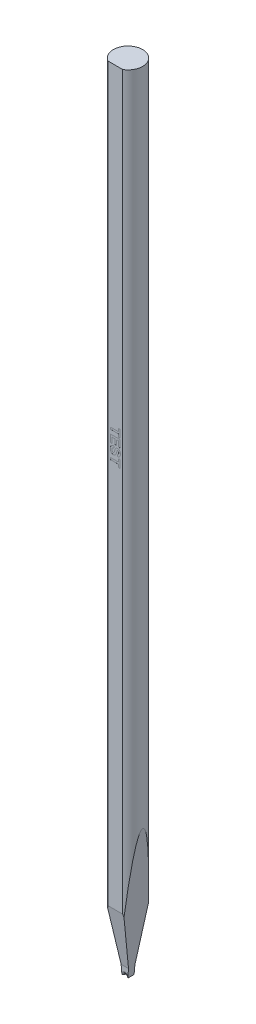
SolidWorks part; units mm, degrees
ref_plane "Ebene vorne" through (0, 0, 0) normal (0, 0, 1) x (1, 0, 0)
ref_plane "Ebene oben" through (0, 0, 0) normal (0, 1, 0) x (1, 0, 0)
ref_plane "Ebene rechts" through (0, 0, 0) normal (1, 0, 0) x (0, 0, -1)
sketch "sketch_TL_cutting" plane through (0, 0, 0) normal (0, 1, 0) x (1, 0, 0)
  circle A0 centre (0, 0) radius 1.4986
extrude "TL_cutting" add sketch "sketch_TL_cutting" along normal blind 81.28
sketch "sketch_TDF_grinding" plane through (0, 0, 0) normal (0, 1, 0) x (1, 0, 0)
  line L0 (0, 0) -> (0, -1.2954) construction
  line L1 (-1.5086, -4.3126) -> (1.5086, -4.3126)
  line L2 (-1.5086, -4.3126) -> (-1.5086, -1.2954)
  line L3 (-1.5086, -1.2954) -> (1.5086, -1.2954)
  line L4 (1.5086, -4.3126) -> (1.5086, -1.2954)
  circle A1 centre (0, 0) radius 1.4986 construction
  point P9 (0, -4.3126)
  dimension "TD_2Offset_X" = 3.0172
  dimension "TD_2Offset_Z" = 3.0172
extrude "TDF_grinding" cut sketch "sketch_TDF_grinding" along normal through all
sketch "sketch_engraving" plane through (0, 0, 1.2954) normal (0, 0, 1) x (1, 0, 0)
  line L0 (0.7535, 81.28) -> (-0.7535, 81.28) construction
  line L6 (-0.7535, 0) -> (0.7535, 0) construction
  line L7 (0, 0) -> (0, 49.28) construction
  line L8 (-0.5, 49.28) -> (-0.5, 0) construction
  text T0 "TEST" font "Arial" height 1
  dimension "D2" = 0.5
  dimension "EngravingStart" = 32
extrude "engraving" cut sketch "sketch_engraving" against normal blind 0.005
sketch "sketch_VW_VR_grinding" plane through (0, 0, 0) normal (0, 0, 1) x (1, 0, 0)
  line L0 (-1.4936, -0.01) -> (-1.4936, 0.874)
  line L1 (1.4936, -0.01) -> (1.4936, 0.874)
  line L2 (-1.4936, 0) -> (1.4936, 0) construction
  line L3 (-1.5086, 0.879) -> (-1.4986, 0.879)
  line L4 (1.4986, 0.879) -> (1.5086, 0.879)
  line L5 (-1.5086, 0.879) -> (-1.5086, -0.01)
  line L6 (-1.5086, -0.01) -> (-1.4936, -0.01)
  line L7 (1.4936, -0.01) -> (1.5086, -0.01)
  line L8 (1.5086, -0.01) -> (1.5086, 0.879)
  line L9 (-1.4986, 0.879) -> (-1.4986, 0.874) construction
  line L10 (-1.4936, 0.874) -> (-1.4986, 0.874) construction
  line L11 (1.4936, 0.874) -> (1.4986, 0.874) construction
  line L12 (1.4986, 0.879) -> (1.4986, 0.874) construction
  arc A0 (-1.4986, 0.879) -> (-1.4936, 0.874) centre (-1.4986, 0.874) cw
  arc A2 (1.4936, 0.874) -> (1.4986, 0.879) centre (1.4986, 0.874) cw
  dimension "D1" = 0.01
  dimension "D4" = 3.0172
extrude "VW_VR_grinding" cut sketch "sketch_VW_VR_grinding" against normal blind 1.5086 and the other way blind 1.5086
sketch "sketch_ISA_grinding" plane through (0, 0, 0) normal (0, 0, 1) x (1, 0, 0)
  line L0 (-0.2997, 0) -> (-1.5086, 13.8176)
  line L4 (1.5086, 13.8176) -> (0.2997, 0)
  line L5 (0.2997, 0) -> (-0.2997, 0)
  line L6 (0, 0) -> (0, 30.49) construction
  line L7 (-1.5086, 13.8176) -> (-1.5086, -0.01)
  line L12 (-1.5086, -0.01) -> (1.5086, -0.01)
  line L13 (1.5086, -0.01) -> (1.5086, 13.8176)
  dimension "ISA" = 10
  dimension "TD_2Offset" = 3.0172
  dimension "Offset" = 0.01
extrude "ISA_grinding" cut sketch "sketch_ISA_grinding" against normal blind 1.5086 and the other way blind 1.5086
sketch "sketch_pre_FRX_BRX" plane through (0, 0, 0) normal (1, 0, 0) x (0, 0, -1)
  line L0 (1.4986, -0.01) -> (1.4986, 3.9152) construction
  line L1 (-1.2954, -0.01) -> (-1.2954, 0.879) construction
  line L2 (-0.3251, -0.01) -> (-0.3251, 0.879)
  line L3 (-0.3251, 0.879) -> (-1.5086, 0.879)
  line L4 (-1.5086, 0.879) -> (-1.5086, -0.01)
  line L5 (-1.5086, -0.01) -> (-0.3251, -0.01)
  line L6 (0.3251, -0.01) -> (0.3251, 0.879)
  line L7 (0.3251, 0.879) -> (1.5086, 0.879)
  line L8 (1.5086, 0.879) -> (1.5086, -0.01)
  line L9 (1.5086, -0.01) -> (0.3251, -0.01)
  dimension "D3" = 0.01
  dimension "D4" = 0.889
  dimension "D5" = 3.0172
  dimension "D6" = 0.6502
  dimension "D2" = 0.01
  dimension "D7" = 1.8237
extrude "pre_FRX_BRX" cut sketch "sketch_pre_FRX_BRX" against normal blind 1.5086 and the other way blind 1.5086
sketch "sketch_contour_V-Groove" plane through (0, 0, 0) normal (1, 0, 0) x (0, 0, -1)
  line L0 (-1.2954, 0.1905) -> (0, 0.1905)
  line L1 (0, 0.1905) -> (1.4986, 0.1905)
  line L2 (1.4986, -0.8411) -> (1.4986, 1.3178) construction
  line L3 (-1.2954, -0.9209) -> (-1.2954, 1.9363) construction
  line L4 (-1.2954, 0) -> (1.4986, 0) construction
  line L5 (0.3251, 0) -> (0.3251, 0.1905) construction
  line L6 (-0.3251, 0) -> (-0.3251, 0.1905) construction
  dimension "D1" = 0
ref_plane "front" through (0, 0, 1.2954) normal (0, 0, 1) x (1, 0, 0)
ref_plane "back" through (0, 0, -1.4986) normal (0, 0, 1) x (1, 0, 0)
sketch "sketch_section_V-Groove" plane through (0, 0, 1.2954) normal (0, 0, 1) x (1, 0, 0)
  line L0 (-1.499, -1.905) -> (-0.0499, 0.1645)
  line L2 (0.0499, 0.1645) -> (1.499, -1.905)
  line L3 (-1.499, -1.905) -> (1.499, -1.905)
  line L4 (0, -1.905) -> (0, 0.1905) construction
  line L5 (-0.1651, 0) -> (0.1651, 0) construction
  arc A0 (0.0499, 0.1645) -> (-0.0499, 0.1645) centre (0, 0.1296) ccw
  dimension "GA" = 70
sweep "V-Groove_EDM" cut profiles "sketch_section_V-Groove" path "sketch_contour_V-Groove"
fillet "FR_EDM" radius 0.2261 3 edges at (0.1075, 0.0823, 0.3251) (0, 0.1905, 0.3251) (-0.1075, 0.0823, 0.3251)
fillet "BR_EDM" radius 0.2261 3 edges at (0.1075, 0.0823, -0.3251) (0, 0.1905, -0.3251) (-0.1075, 0.0823, -0.3251)
sketch "sketch_FA_BA_grinding" plane through (0, 0, 0) normal (1, 0, 0) x (0, 0, -1)
  line L2 (2.4986, 13.2154) -> (2.4986, -0.1)
  line L3 (2.4986, -0.1) -> (0.3251, -0.1)
  line L5 (0.3251, -0.1) -> (0.3251, 0.889)
  line L6 (0.3251, 0.889) -> (2.4986, 13.2154)
  line L7 (1.4986, -0.1) -> (1.4986, 7.5441) construction
  line L8 (-1.2954, 6.3917) -> (-1.2954, -0.1) construction
  line L9 (-4.003, 21.7474) -> (-0.3251, 0.889)
  line L10 (-0.3251, 0.889) -> (-0.3251, -0.1)
  line L11 (-0.3251, -0.1) -> (-4.003, -0.1)
  line L12 (-4.003, -0.1) -> (-4.003, 21.7474)
  line L13 (-0.3251, 0.889) -> (0.3251, 0.889) construction
  dimension "D4" = 1
  dimension "D1" = 0.1
  dimension "FA" = 10
  dimension "BA" = 10
extrude "FA_BA_grinding" cut sketch "sketch_FA_BA_grinding" against normal blind 1.5086 and the other way blind 1.5086
sketch "sketch_groove_dimensions" plane through (0, 0, 0) normal (1, 0, 0) x (0, 0, -1)
  line L0 (-0.0991, 0.1905) -> (0.0991, 0.1905)
  line L1 (-0.3251, 0) -> (-0.3251, 0.4166) construction
  line L2 (1.4986, 0) -> (1.4986, 0.4166) construction
  line L3 (0.3251, 0) -> (0.3251, 0.4166) construction
  line L4 (-1.2954, 0) -> (-1.2954, 0.3999) construction
  arc A0 (0.0991, 0.1905) -> (0.3251, 0.4166) centre (0.0991, 0.4166) ccw
  arc A1 (-0.0991, 0.1905) -> (-0.3251, 0.4166) centre (-0.0991, 0.4166) cw
equation "\"_Offset\"=0.01mm"
equation "\"TL\"=81.28mm"
equation "\"TD\"=2.9972mm"
equation "\"TDF\"=2.794mm"
equation "\"BA\"=10deg"
equation "\"ISA\"=10deg"
equation "\"FA\"=10deg"
equation "\"GR\"=0.06096mm"
equation "\"GA\"=70deg"
equation "\"GD\"=0.1905mm"
equation "\"FL\"=0.65024mm"
equation "\"F\"=0.35052mm"
equation "\"FX\"=0mm"
equation "\"B\"=0.3302mm"
equation "\"VW\"=0mm"
equation "\"cleaned_VR\"= IIF ( \"VR\" > 0 , \"VR\" , \"E\" - \"_Offset\" )"
equation "\"cleaned_VW\"= IIF ( \"VW\" > 0 , \"VW\" , \"TD\" - \"_Offset\" )"
equation "\"back_edge\"= \"TD\" / 2 - \"X\""
equation "\"side_edge_Offset\"= \"TD\" / 2 + \"_Offset\""
equation "\"TD@sketch_TL_cutting\"=\"TD\""
equation "\"TL@TL_cutting\"=\"TL\""
equation "\"TDF@sketch_TDF_grinding\"=\"TDF\""
equation "\"TD_2Offset_X@sketch_TDF_grinding\"=\"TD\"+2*\"_Offset\""
equation "\"TD_2Offset_Z@sketch_TDF_grinding\"=\"TD\"+2*\"_Offset\""
equation "\"TL_Offset\"= \"TL\" + \"_Offset\""
equation "\"ISA@sketch_ISA_grinding\"=\"ISA\""
equation "\"W@sketch_ISA_grinding\"=\"W\""
equation "\"TD_2Offset@sketch_ISA_grinding\"=\"TD\"+2*\"_Offset\""
equation "\"Offset@sketch_ISA_grinding\"=\"_Offset\""
equation "\"05TD_Offset_posZ@ISA_grinding\"=\"side_edge_Offset\""
equation "\"05TD_Offset_negZ@ISA_grinding\"=\"side_edge_Offset\""
equation "\"E\"=0.889mm"
equation "\"cleaned_X\"= IIF ( \"X\" > 0 , \"X\" , \"TD\" / 2 - \"FL\" / 2 )"
equation "\"FR\"=0.22606mm"
equation "\"BR\"=0.22606mm"
equation "\"D1\"= \"side_edge_Offset\""
equation "\"D2\"= \"side_edge_Offset\""
equation "\"TDF@sketch_FA_BA_grinding\" = \"TDF\""
equation "\"FL@sketch_FA_BA_grinding\"=\"FL\""
equation "\"E@sketch_FA_BA_grinding\" = \"E\""
equation "\"D1@FA_BA_grinding\"=\"side_edge_Offset\""
equation "\"D2@FA_BA_grinding\"=\"side_angle_Offset\""
equation "\"10GD@sketch_section_V-Groove\" = 10 * \"GD\""
equation "\"GA@sketch_section_V-Groove\" = \"GA\""
equation "\"GD@sketch_section_V-Groove\" = \"GD\""
equation "\"B@sketch_section_V-Groove\" = \"B\""
equation "\"GD@sketch_contour_V-Groove\" = \"GD\""
equation "\"cleaned_FRX\"= IIF ( \"FRX\" > 0 , \"FRX\" , \"FR\" )"
equation "\"cleaned_BRX\"= IIF ( \"BRX\" > 0 , \"BRX\" , \"BR\" )"
equation "\"FL_groove_angle\"=0deg"
equation "\"D3@sketch_pre_FRX_BRX\" = \"_Offset\""
equation "\"D4@sketch_pre_FRX_BRX\" = \"E\""
equation "\"D5@sketch_pre_FRX_BRX\" = 2 * \"side_edge_Offset\""
equation "\"D6@sketch_pre_FRX_BRX\" = \"FL\" + ( \"FR\" - \"cleaned_FRX\" ) + ( \"BR\" - \"cleaned_BRX\" )"
equation "\"TD/2@sketch_pre_FRX_BRX\" = \"TD\" / 2"
equation "\"TDF@sketch_pre_FRX_BRX\" = \"TDF\""
equation "\"D2@sketch_pre_FRX_BRX\" = \"_Offset\""
equation "\"D1@pre_FRX_BRX\" = \"side_edge_Offset\""
equation "\"D2@pre_FRX_BRX\" = \"side_edge_Offset\""
equation "\"D1@BR_EDM\"=\"BR\""
equation "\"TD/2@sketch_FA_BA_grinding\" = \"TD\" / 2"
equation "\"TD/2@sketch_contour_V-Groove\" = \"TD\" / 2"
equation "\"TDF@sketch_contour_V-Groove\" = \"TDF\""
equation "\"D1@sketch_contour_V-Groove\"=\"FL_groove_angle\""
equation "\"FL@sketch_contour_V-Groove\"=\"FL\""
equation "\"FL/2@sketch_contour_V-Groove\" = \"FL\" / 2"
equation "\"D1@FR_EDM\"=\"FR\""
equation "\"D1@sketch_VW_VR_grinding\" = \"_Offset\""
equation "\"D4@sketch_VW_VR_grinding\" = 2 * \"side_edge_Offset\""
equation "\"VR@sketch_VW_VR_grinding\" = \"cleaned_VR\""
equation "\"VW@sketch_VW_VR_grinding\"=\"cleaned_VW\""
equation "\"D1@VW_VR_grinding\" = \"side_edge_Offset\""
equation "\"D2@VW_VR_grinding\" = \"side_edge_Offset\""
equation "\"X\"=0mm"
equation "\"VR\"=0mm"
equation "\"W\"=0.59944mm"
equation "\"VW_radius\"= \"cleaned_VW\" / 10"
equation "\"VW_radius_cleaned\"= IIF ( \"VW\" > 0 , \"VW_radius\" , \"_Offset\" / 2 )"
equation "\"D2@sketch_VW_VR_grinding\"=\"VW_radius_cleaned\""
equation "\"FRX\"=0mm"
equation "\"BRX\"=0mm"
equation "\"FA@sketch_FA_BA_grinding\" = \"FA\""
equation "\"D4@sketch_FA_BA_grinding\"=\"_Offset\"*100"
equation "\"BA@sketch_FA_BA_grinding\" = \"BA\""
equation "\"D1@sketch_groove_dimensions\" = \"TD\" / 2"
equation "\"FL@sketch_groove_dimensions\" = \"FL\""
equation "\"FR@sketch_groove_dimensions\" = \"FR\""
equation "\"BR@sketch_groove_dimensions\" = \"BR\""
equation "\"FRX@sketch_groove_dimensions\" = \"cleaned_FRX\""
equation "\"BRX@sketch_groove_dimensions\" = \"cleaned_BRX\""
equation "\"GD@sketch_groove_dimensions\" = \"GD\""
equation "\"cleaned_FX\"= IIF ( \"FX\" > 0 , \"FX\" , \"TDF\" - ( \"TD\" + \"FL\" ) / 2 )"
equation "\"D7@sketch_pre_FRX_BRX\"=\"TDF\"-\"cleaned_FX\"-(\"FR\"-\"cleaned_FRX\")"
equation "\"FX@sketch_contour_V-Groove\" = \"cleaned_FX\""
equation "\"FX@sketch_FA_BA_grinding\" = \"cleaned_FX\""
equation "\"TDF@sketch_groove_dimensions\" = \"TDF\""
equation "\"FX@sketch_groove_dimensions\" = \"cleaned_FX\""
equation "\"EngravingStart\" =32mm"
equation "\"EngravingStart@sketch_engraving\" = \"EngravingStart\""
